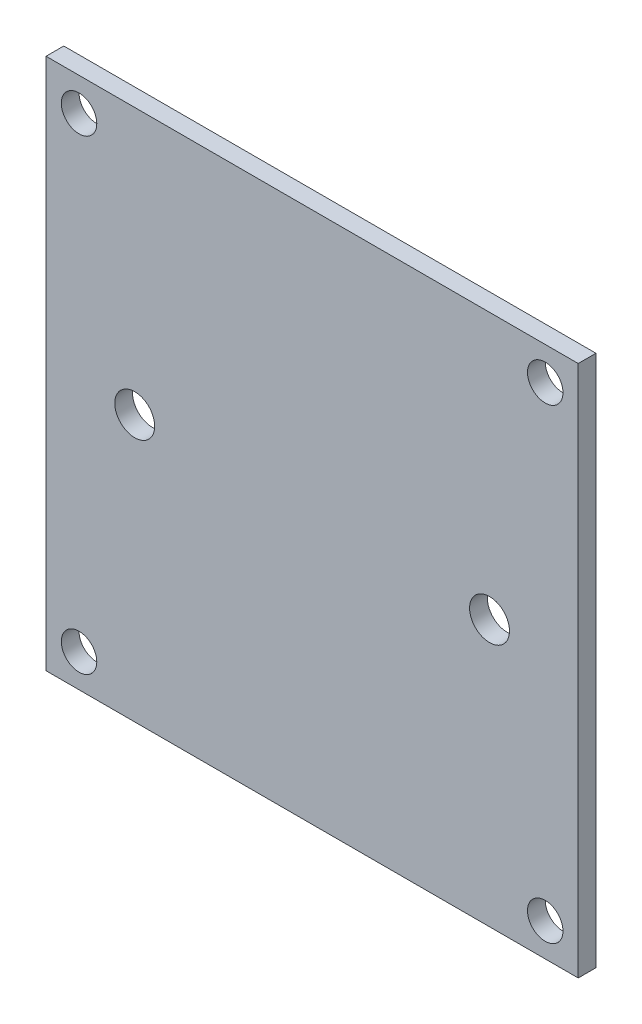
SolidWorks part; units mm, degrees
ref_plane "Front Plane" through (0, 0, 0) normal (0, 0, 1) x (1, 0, 0)
ref_plane "Top Plane" through (0, 0, 0) normal (0, 1, 0) x (1, 0, 0)
ref_plane "Right Plane" through (0, 0, 0) normal (1, 0, 0) x (0, 0, -1)
sketch "Sketch1" plane through (0, 0, 0) normal (0, 0, 1) x (1, 0, 0)
  line L1 (15, 15) -> (-15, 15)
  line L2 (15, 15) -> (15, -15)
  line L3 (15, -15) -> (-15, -15)
  line L4 (-15, 15) -> (-15, -15)
  line L5 (15, 15) -> (-15, -15) construction
  line L6 (15, -15) -> (-15, 15) construction
  point P0 (0, 0)
  dimension "D1" = 30
  dimension "D2" = 30
extrude "Boss-Extrude1" add sketch "Sketch1" along normal blind 1
sketch "Sketch2" plane through (0, 0, 1) normal (0, 0, 1) x (1, 0, 0)
  line L0 (-15, 15) -> (-15, -15) construction
  line L1 (15, 15) -> (-15, 15) construction
  line L2 (15, -15) -> (15, 15) construction
  line L3 (-15, -15) -> (15, -15) construction
  circle A0 centre (-13.14, 13.14) radius 1
  circle A1 centre (13.14, 13.14) radius 1
  circle A2 centre (13.14, -13.14) radius 1
  circle A3 centre (-13.14, -13.14) radius 1
  circle A4 centre (-10, 0) radius 1.125
  circle A5 centre (10, 0) radius 1.125
  dimension "D1" = 2
  dimension "D2" = 1.86
  dimension "D4" = 1.86
  dimension "D8" = 2.25
  dimension "D3" = 1.86
  dimension "D5" = 1.86
  dimension "D6" = 5
  dimension "D7" = 5
extrude "Cut-Extrude1" cut sketch "Sketch2" against normal through all
